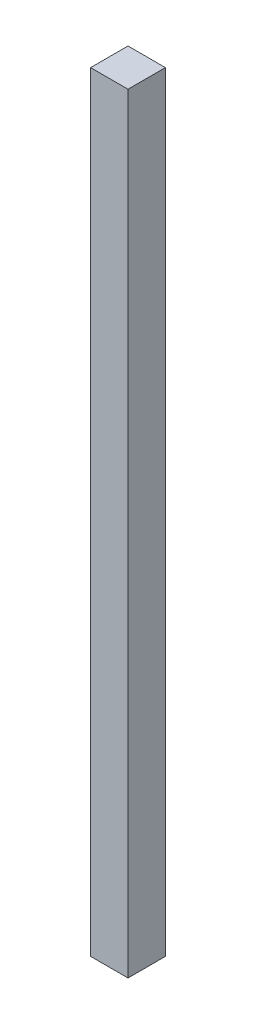
SolidWorks part; units mm, degrees
ref_plane "Front Plane" through (0, 0, 0) normal (0, 0, 1) x (1, 0, 0)
ref_plane "Top Plane" through (0, 0, 0) normal (0, 1, 0) x (1, 0, 0)
ref_plane "Right Plane" through (0, 0, 0) normal (1, 0, 0) x (0, 0, -1)
sketch "Sketch1" plane through (0, 0, 0) normal (0, 1, 0) x (1, 0, 0)
  line L0 (0, 0) -> (0, 88.9)
  line L1 (0, 88.9) -> (-88.9, 88.9)
  line L2 (-88.9, 88.9) -> (-88.9, 0)
  line L3 (-88.9, 0) -> (0, 0)
extrude "Boss-Extrude1" add sketch "Sketch1" along normal blind 1828.8 contours L1 L2 L3 L0
